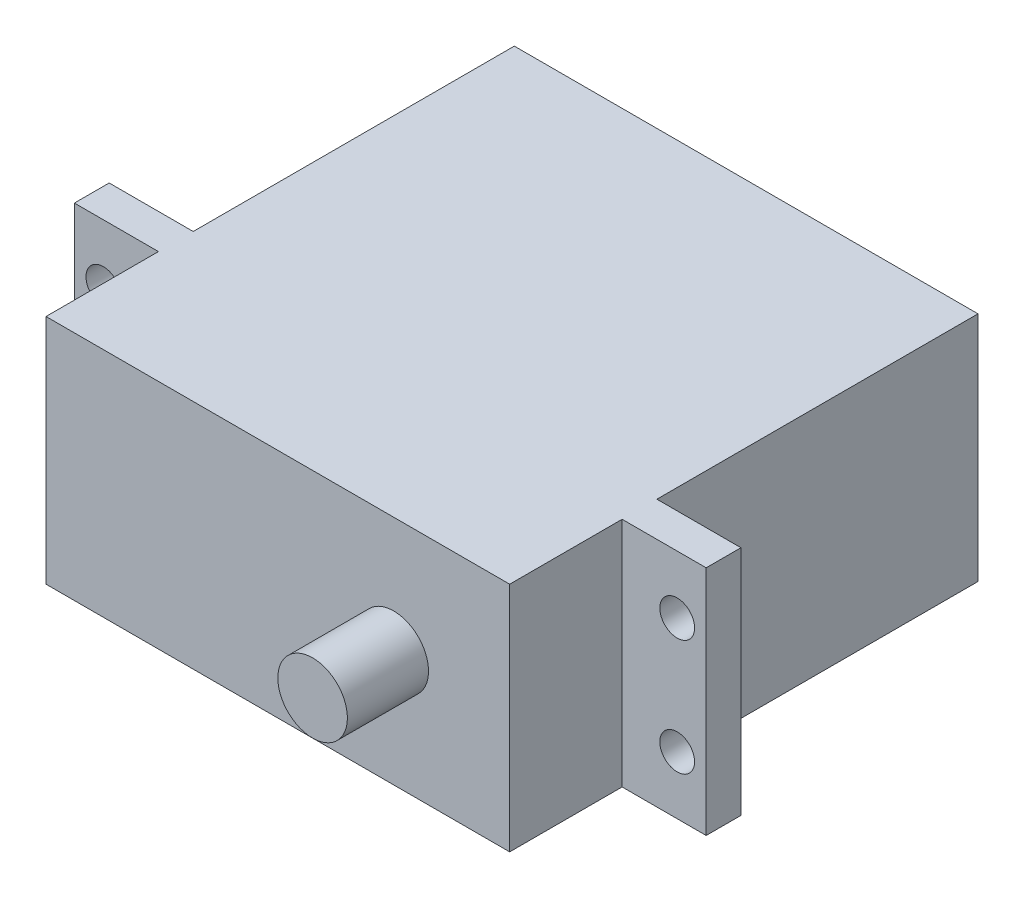
SolidWorks part; units mm, degrees
ref_plane "Front Plane" through (0, 0, 0) normal (0, 0, 1) x (1, 0, 0)
ref_plane "Top Plane" through (0, 0, 0) normal (0, 1, 0) x (1, 0, 0)
ref_plane "Right Plane" through (0, 0, 0) normal (1, 0, 0) x (0, 0, -1)
sketch "Sketch1" plane through (0, 0, 0) normal (0, 1, 0) x (1, 0, 0)
  line L1 (-27.6845, 15.2601) -> (12.3155, 15.2601)
  line L2 (-27.6845, 15.2601) -> (-27.6845, -25.1399)
  line L3 (-27.6845, -25.1399) -> (12.3155, -25.1399)
  line L4 (12.3155, 15.2601) -> (12.3155, -25.1399)
  dimension "D1" = 40
  dimension "D2" = 40.4
extrude "Boss-Extrude1" add sketch "Sketch1" along normal blind 20
sketch "Sketch3" plane through (12.3155, 0, 0) normal (1, 0, 0) x (0, 0, -1)
  line L0 (-25.1399, 20) -> (15.2601, 20) construction
  line L1 (-25.1399, 0) -> (15.2601, 0) construction
  line L2 (-15.4399, 20) -> (-12.4399, 20)
  line L3 (-15.4399, 20) -> (-15.4399, 0)
  line L4 (-15.4399, 0) -> (-12.4399, 0)
  line L5 (-12.4399, 20) -> (-12.4399, 0)
  line L7 (15.2601, 20) -> (15.2601, 0) construction
  dimension "D1" = 27.7
  dimension "D2" = 3
extrude "Boss-Extrude2" add sketch "Sketch3" along normal blind 7.25
sketch "Sketch4" plane through (0, 0, 0) normal (0, -1, 0) x (-1, 0, 0)
  line L0 (7.6845, -25.1399) -> (7.6845, 15.2601) construction
  line L1 (27.6845, -25.1399) -> (-12.3155, -25.1399) construction
  line L2 (-12.3155, 15.2601) -> (27.6845, 15.2601) construction
ref_plane "Plane1" through (-7.6845, 0, 0) normal (-1, 0, 0) x (0, 0, 1)
mirror "Mirror1" about plane through (-7.6845, 0, 0) normal (-1, 0, 0) of "Boss-Extrude2"
sketch "Sketch5" plane through (0, 0, 15.4399) normal (0, 0, 1) x (1, 0, 0)
  line L5 (-32.4345, 15) -> (17.0655, 15) construction
  line L6 (17.0655, 5) -> (-32.4345, 5) construction
  circle A0 centre (17.0655, 15) radius 1.5
  circle A1 centre (17.0655, 5) radius 1.5
  circle A2 centre (-32.4345, 15) radius 1.5
  circle A3 centre (-32.4345, 5) radius 1.5
  dimension "D2" = 3
  dimension "D3" = 3
  dimension "D4" = 3
  dimension "D5" = 3
  dimension "D1" = 10
  dimension "D6" = 49.5
  dimension "D10" = 10
  dimension "D11" = 49.5
extrude "Cut-Extrude1" cut sketch "Sketch5" against normal blind 7.25
sketch "Sketch6" plane through (0, 0, 25.1399) normal (0, 0, 1) x (1, 0, 0)
  line L0 (-27.6845, 20) -> (12.3155, 20) construction
  line L1 (-27.6845, 20) -> (-27.6845, 0) construction
  circle A0 centre (2.3155, 10) radius 3
  dimension "D1" = 10
  dimension "D2" = 30
extrude "Boss-Extrude3" add sketch "Sketch6" along normal blind 7
